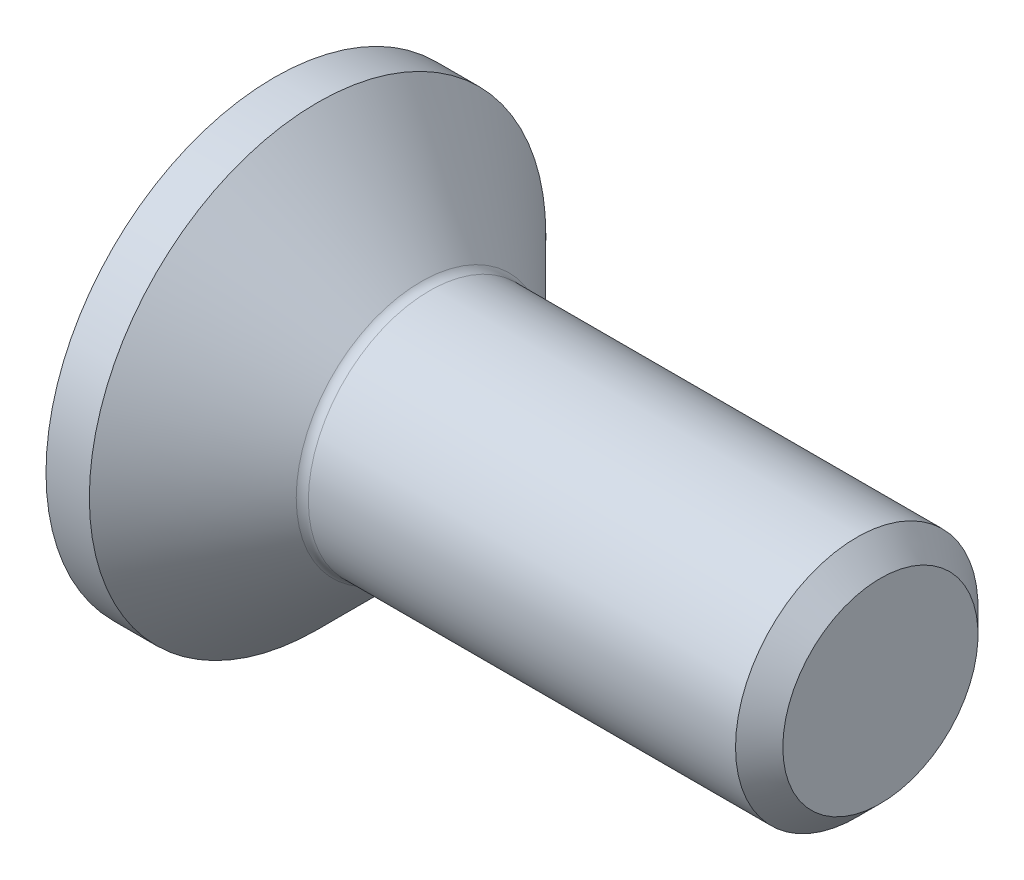
SolidWorks part; units mm, degrees
ref_plane "Plane1" through (0, 0, 0) normal (0, 0, 1) x (1, 0, 0)
ref_plane "Plane2" through (0, 0, 0) normal (0, 1, 0) x (1, 0, 0)
ref_plane "Plane3" through (0, 0, 0) normal (1, 0, 0) x (0, 0, -1)
revolve "BaseBody" add sketch "BodySke"
sketch "BodySke" plane through (0, 0, 0) normal (0, 0, 1) x (1, 0, 0)
  line L0 (0, 0) -> (0, 3.765)
  line L1 (0.715, 3.765) -> (2.48, 2)
  line L2 (0, 3.765) -> (0.715, 3.765)
  line L3 (2.48, 2) -> (9.61, 2)
  line L4 (10, 1.61) -> (10, 0)
  line L5 (10, 0) -> (0, 0)
  line L6 (0, 0) -> (127, 0) construction
  line L7 (0.715, -3.765) -> (2.48, -2) construction
  line L8 (10, 1.61) -> (9.61, 2)
  line L9 (0, -3.765) -> (0.715, -3.765) construction
  line L10 (10, -1.61) -> (9.61, -2) construction
  line L11 (3.18, 8.35) -> (3.18, -13.875) construction
  line L12 (0, 19.05) -> (0, -3.175) construction
  dimension "D1" = 0.715
  dimension "Diameter" = 4
  dimension "Head_ht" = 2.48
  dimension "Length" = 10
  dimension "Body_ch_ang" = 45
  dimension "Head_dia" = 7.53
  dimension "Minor_dia" = 3.22
  dimension "Head_ang" = 90
  dimension "Advance" = 0.7
  dimension "Thread_nom" = 10
cosmetic thread "ThreadCosmetic"
fillet "Fillet1" radius 0.2 1 edges at (2.48, 0, 2)
sketch "Sketch2" plane through (0, 0, 0) normal (0, 0, 1) x (1, 0, 0)
  line L0 (0, 1.25) -> (1.5, 1.25)
  line L1 (1.5, 1.25) -> (2.2217, 0)
  line L2 (0, 0) -> (127, 0) construction
  line L3 (2.2217, 0) -> (0, 0)
  line L4 (0, 0) -> (0, 1.25)
  line L5 (0, -1.25) -> (1.5, -1.25) construction
  line L6 (0, 0) -> (47.625, 0) construction
  line L8 (0, 3.765) -> (0, -3.765) construction
  dimension "D2" = 60
  dimension "PreBroach_depth" = 1.5
  dimension "PreBroach_dia" = 2.5
revolve "PreBroach" cut sketch "Sketch2" angle 360 about L6
sketch "Sketch3" plane through (0, 0, 0) normal (-1, 0, 0) x (0, 0, 1)
  line L0 (-1.25, -0.7217) -> (-1.25, 0.7217)
  line L1 (-1.25, 0.7217) -> (0, 1.4434)
  line L2 (0, 1.4434) -> (1.25, 0.7217)
  line L3 (1.25, 0.7217) -> (1.25, -0.7217)
  line L4 (1.25, -0.7217) -> (0, -1.4434)
  line L5 (0, -1.4434) -> (-1.25, -0.7217)
  dimension "D1" = 1.25
  dimension "D2" = 1.25
  dimension "D3" = 2.5
  dimension "Hex_size" = 2.5
extrude "Hex" cut sketch "Sketch3" against normal blind 1.5
sketch "ThdSchSke" plane through (0, 0, 0) normal (0, 0, 1) x (1, 0, 0)
  line L0 (4.58, -1.61) -> (4.3069, -2)
  line L1 (4.58, -1.61) -> (4.8531, -2)
  line L2 (4.8531, -2) -> (4.8531, -2.5)
  line L3 (-3.175, 0) -> (5.1513, 0) construction
  line L4 (0, 3.765) -> (0, -3.765) construction
  line L5 (4.8531, -2.5) -> (4.3069, -2.5)
  line L6 (4.3069, -2.5) -> (4.3069, -2)
  dimension "Thread_minor" = 3.22
  dimension "Diameter" = 4
  dimension "Start" = 4.58
  dimension "SideAngle" = 55
  dimension "VeeAngle" = 70
  dimension "Overcut" = 5
revolve "ThreadSchematic" cut sketch "ThdSchSke" angle 360 about L3
pattern_linear "ThdSchPat"
equation "\"Thread_minor@ThreadCosmetic\"  =  \"Minor_dia@BodySke\""
equation "\"D1@Sketch3\" = \"Hex_size@Sketch3\" / 2"
equation "\"D2@Sketch3\" = \"D1@Sketch3\""
equation "\"D3@Sketch3\" = \"Hex_size@Sketch3\""
equation "\"Thread_length@ThreadCosmetic\" = ((sgn( (\"Length@BodySke\" - \"Advance@BodySke\" * 3.0 - \"Head_ht@BodySke\" ) - \"Thread_nom@BodySke\" )-1)*( (\"Length@BodySke\" - \"Advance@BodySke\" * 3.0 - \"Head_ht@BodySke\" ) - \"Thread_nom@BodySke\" ))/-2+ \"Thread_nom@BodySke\""
equation "\"Thread_minor@ThdSchSke\" = \"Minor_dia@BodySke\""
equation "\"Diameter@ThdSchSke\" = \"Diameter@BodySke\""
equation "\"Overcut@ThdSchSke\" = \"Diameter@BodySke\" * 1.25"
equation "\"Start@ThdSchSke\" = 0.000001 + \"Length@BodySke\" - \"Thread_length@ThreadCosmetic\"  '---Countersunk---"
equation "\"Num_threads@ThdSchPat\" = int( \"Thread_length@ThreadCosmetic\" / \"Advance@BodySke\" + 0.999 )  + 1"
equation "\"Advance@ThdSchPat\" = \"Thread_length@ThreadCosmetic\" /  (\"Num_threads@ThdSchPat\" - 1) 'relax it"
equation "\"Num_threads@ThdSchPat\" = \"Num_threads@ThdSchPat\" - sgn( \"Num_threads@ThdSchPat\" - 1) '---chamfered tips only---"
